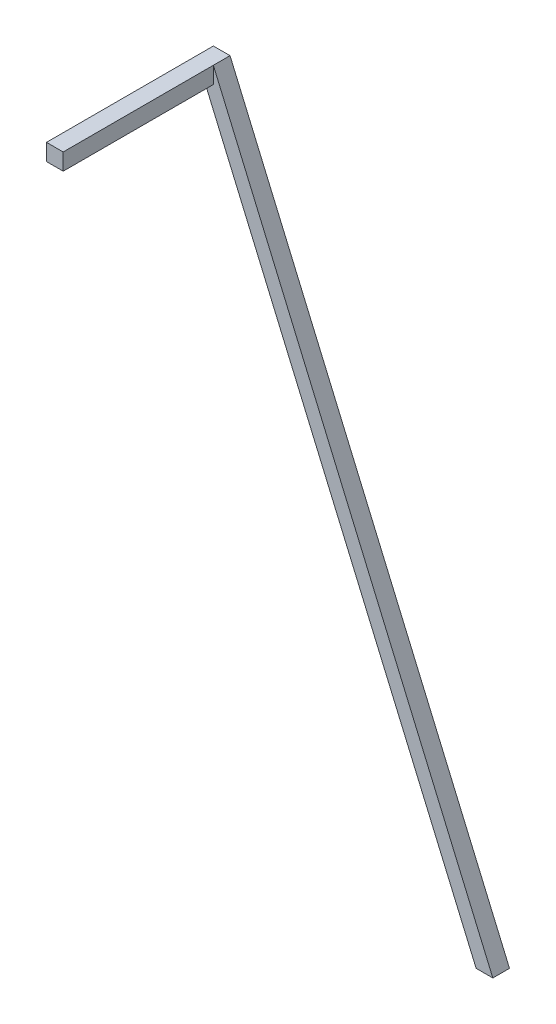
SolidWorks part; units mm, degrees
ref_plane "Front Plane" through (0, 0, 0) normal (0, 0, 1) x (1, 0, 0)
ref_plane "Top Plane" through (0, 0, 0) normal (0, 1, 0) x (1, 0, 0)
ref_plane "Right Plane" through (0, 0, 0) normal (1, 0, 0) x (0, 0, -1)
sketch "Sketch1" plane through (0, 0, 0) normal (0, 0, 1) x (1, 0, 0)
  line L1 (-12.7, -12.7) -> (12.7, -12.7)
  line L2 (-12.7, -12.7) -> (-12.7, 12.7)
  line L3 (-12.7, 12.7) -> (12.7, 12.7)
  line L4 (12.7, -12.7) -> (12.7, 12.7)
  line L5 (-12.7, -12.7) -> (12.7, 12.7) construction
  line L6 (-12.7, 12.7) -> (12.7, -12.7) construction
  point P0 (0, 0)
  dimension "D1" = 25.4
  dimension "D2" = 25.4
extrude "Boss-Extrude1" add sketch "Sketch1" along normal blind 254
sketch "Sketch2" plane through (0, 0, 0) normal (0, 0, 1) x (1, 0, 0)
  line L0 (12.7, 12.7) -> (438.15, -977.9)
  line L1 (12.7, 12.7) -> (-12.7, 12.7) construction
  line L2 (12.7, -12.7) -> (12.7, 12.7) construction
  line L3 (412.75, -977.9) -> (-1.791, -12.7)
  line L4 (412.75, -977.9) -> (438.15, -977.9)
  line L5 (12.7, 12.7) -> (12.7, -12.7)
  line L6 (-12.7, -12.7) -> (12.7, -12.7) construction
  line L8 (-1.791, -12.7) -> (12.7, -12.7)
  dimension "D1" = 990.6
  dimension "D2" = 425.45
  dimension "D3" = 25.4
extrude "Boss-Extrude2" add sketch "Sketch2" along normal blind 25.4 separate body
sketch "Sketch3" plane through (0, 0, 0) normal (0, 0, 1) x (1, 0, 0)
  line L0 (438.15, -977.9) -> (438.15, -768.9364)
